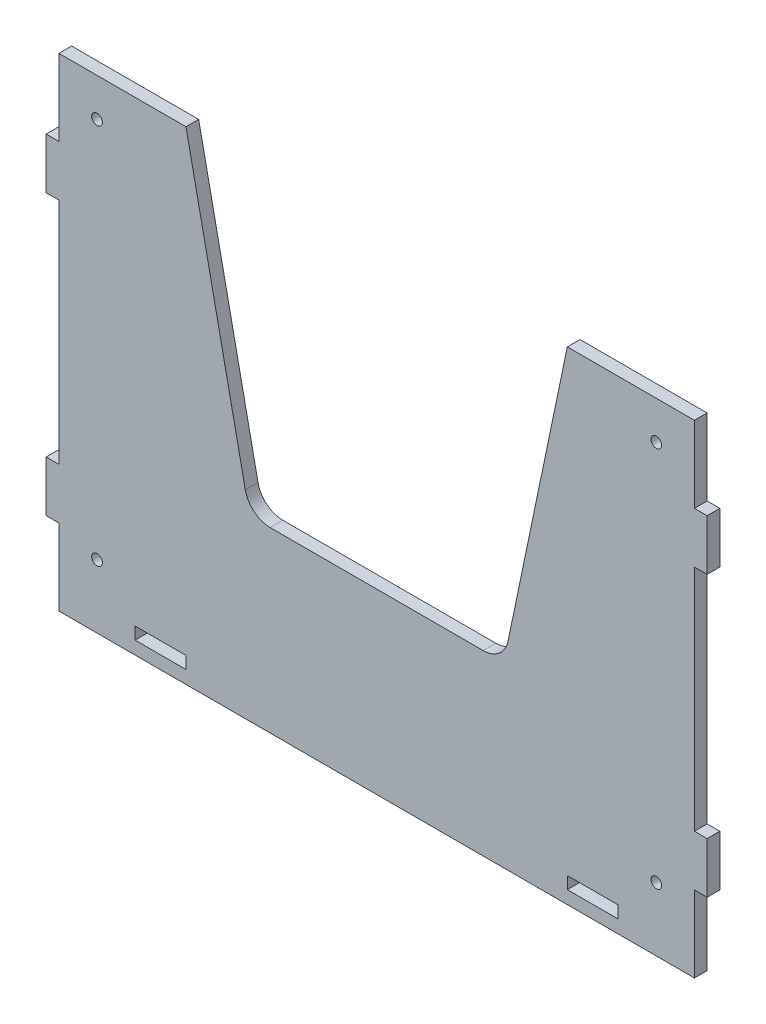
SolidWorks part; units mm, degrees
ref_plane "Front Plane" through (0, 0, 0) normal (0, 0, 1) x (1, 0, 0)
ref_plane "Top Plane" through (0, 0, 0) normal (0, 1, 0) x (1, 0, 0)
ref_plane "Right Plane" through (0, 0, 0) normal (1, 0, 0) x (0, 0, -1)
sketch "Sketch1" plane through (0, 0, 0) normal (0, 0, 1) x (1, 0, 0)
  line L0 (-125, -10) -> (-125, 273) construction
  line L1 (125, -10) -> (-125, -10)
  line L2 (125, -10) -> (125, 20)
  line L3 (125, -10) -> (125, 273) construction
  line L4 (-125, -10) -> (-125, 20)
  line L5 (125, 180) -> (75, 180)
  line L6 (75, 180) -> (50, 60)
  line L7 (50, 60) -> (-50, 60)
  line L8 (-50, 60) -> (-75, 180)
  line L9 (-75, 180) -> (-125, 180)
  line L12 (95, 0) -> (95, -5) construction
  line L13 (95, -4.9) -> (75, -4.9)
  line L14 (95, -4.9) -> (95, -0.1)
  line L15 (95, -0.1) -> (75, -0.1)
  line L16 (75, -4.9) -> (75, -0.1)
  line L17 (75, 0) -> (75, -5) construction
  line L18 (95, 0) -> (75, 0) construction
  line L19 (-75, 0) -> (-75, -5) construction
  line L20 (-75, -4.9) -> (-95, -4.9)
  line L21 (-75, -4.9) -> (-75, -0.1)
  line L22 (-75, -0.1) -> (-95, -0.1)
  line L23 (-95, -4.9) -> (-95, -0.1)
  line L24 (-95, 0) -> (-95, -5) construction
  line L25 (-75, 0) -> (-95, 0) construction
  line L26 (-130, -10) -> (-130, 273) construction
  line L27 (-125, 20) -> (-130, 20)
  line L28 (130, -10) -> (130, 273) construction
  line L29 (-125, 40) -> (-130, 40)
  line L30 (-130, 20) -> (-130, 40)
  line L31 (-125, 150) -> (-125, 180)
  line L32 (-125, 130) -> (-130, 130)
  line L33 (-125, 40) -> (-125, 130)
  line L34 (-125, 150) -> (-130, 150)
  line L35 (-130, 130) -> (-130, 150)
  line L36 (125, 40) -> (130, 40)
  line L38 (125, 20) -> (130, 20)
  line L39 (130, 40) -> (130, 20)
  line L40 (125, 150) -> (125, 180)
  line L41 (125, 150) -> (130, 150)
  line L42 (125, 40) -> (125, 130)
  line L43 (125, 130) -> (130, 130)
  line L44 (130, 150) -> (130, 130)
  dimension "D1" = 50
  dimension "D2" = 50
  dimension "D3" = 100
  dimension "D4" = 50
  dimension "D5" = 190
  dimension "D6" = 70
  dimension "D7" = 4.8
  dimension "D8" = 0.1
  dimension "D9" = 4.8
  dimension "D10" = 0.1
  dimension "D11" = 20
  dimension "D12" = 20
  dimension "D13" = 30
  dimension "D14" = 30
  dimension "D15" = 20
  dimension "D16" = 20
  dimension "D17" = 30
  dimension "D18" = 30
extrude "Boss-Extrude1" add sketch "Sketch1" along normal blind 5
fillet "Fillet1" radius 10 2 edges at (50, 60, 2.5) (-50, 60, 2.5)
sketch "Sketch2" plane through (0, 0, 5) normal (0, 0, 1) x (1, 0, 0)
  line L0 (-125, -10) -> (125, -10) construction
  line L1 (-125, 20) -> (-125, -10) construction
  line L2 (125, -10) -> (125, 20) construction
  line L4 (-75, 180) -> (-125, 180) construction
  line L5 (125, 180) -> (75, 180) construction
  circle A0 centre (-110, 15) radius 2.1
  circle A1 centre (110, 15) radius 2.1
  circle A2 centre (110, 165) radius 2.1
  circle A3 centre (-110, 165) radius 2.1
  dimension "D1" = 4.2
  dimension "D2" = 4.2
  dimension "D3" = 25
  dimension "D5" = 25
  dimension "D6" = 15
  dimension "D7" = 4.2
  dimension "D8" = 4.2
  dimension "D9" = 15
  dimension "D4" = 15
  dimension "D10" = 15
extrude "Cut-Extrude1" cut sketch "Sketch2" against normal blind 5
